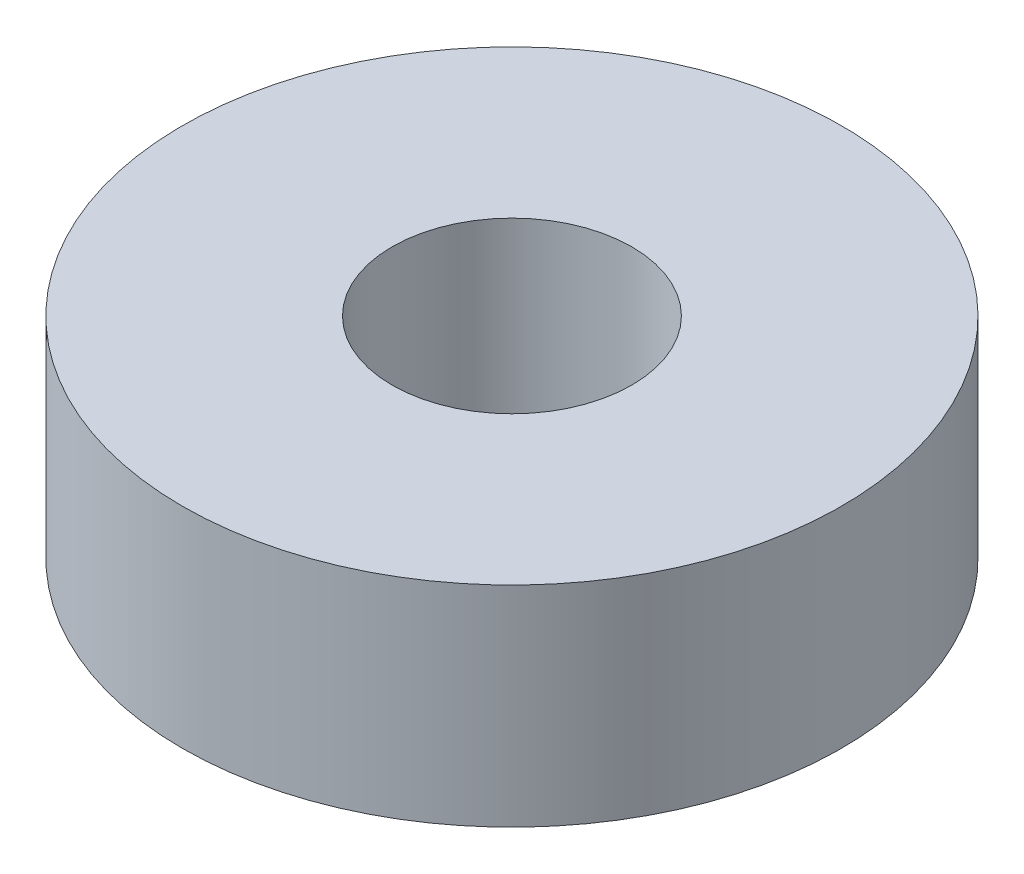
SolidWorks part; units mm, degrees
ref_plane "Front Plane" through (0, 0, 0) normal (0, 0, 1) x (1, 0, 0)
ref_plane "Top Plane" through (0, 0, 0) normal (0, 1, 0) x (1, 0, 0)
ref_plane "Right Plane" through (0, 0, 0) normal (1, 0, 0) x (0, 0, -1)
sketch "Sketch1" plane through (0, 0, 0) normal (0, 1, 0) x (1, 0, 0)
  circle A0 centre (0, 0) radius 11
  circle A1 centre (0, 0) radius 4
extrude "Boss-Extrude1" add sketch "Sketch1" along normal blind 7
